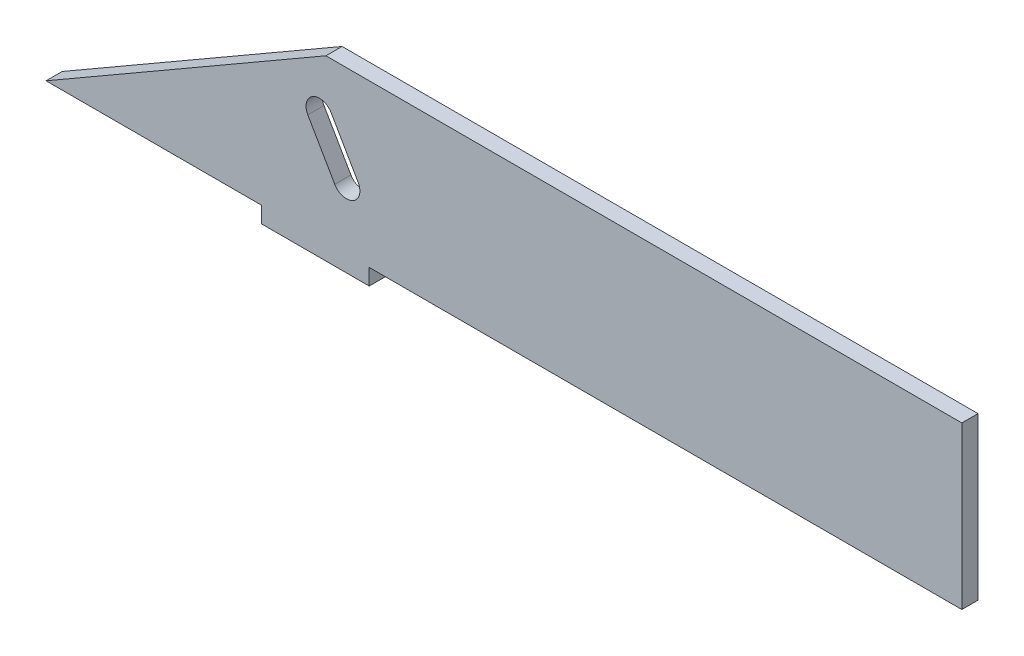
SolidWorks part; units mm, degrees
ref_plane "Front Plane" through (0, 0, 0) normal (0, 0, 1) x (1, 0, 0)
ref_plane "Top Plane" through (0, 0, 0) normal (0, 1, 0) x (1, 0, 0)
ref_plane "Right Plane" through (0, 0, 0) normal (1, 0, 0) x (0, 0, -1)
sketch "Sketch1" plane through (0, 0, 0) normal (0, 0, 1) x (1, 0, 0)
  line L0 (-10, -15) -> (-10, -18)
  line L1 (50, -15) -> (10, -15)
  line L2 (50, -15) -> (50, 15)
  line L3 (50, 15) -> (-50, 15)
  line L4 (-50, -15) -> (-50, 15)
  line L5 (50, -15) -> (-50, 15) construction
  line L6 (50, 15) -> (-50, -15) construction
  line L7 (-10, -18) -> (10, -18)
  line L8 (10, -18) -> (10, -15)
  line L9 (-10, -15) -> (-50, -15)
  point P0 (0, 0)
  dimension "D1" = 100
  dimension "D2" = 30
  dimension "D3" = 3
  dimension "D4" = 20
  dimension "D5" = 40
extrude "Boss-Extrude1" add sketch "Sketch1" along normal blind 3
sketch "Sketch4" plane through (0, 0, 3) normal (0, 0, 1) x (1, 0, 0)
  line L0 (-50, -15) -> (1.9615, 15)
  line L1 (50, 15) -> (-50, 15) construction
  line L2 (-50, 15) -> (-50, -15) construction
  line L3 (1.9615, 15) -> (-50, 15)
  line L4 (-50, 15) -> (-50, -14.2203)
  dimension "D1" = 60
extrude "Cut-Extrude3" cut sketch "Sketch4" against normal blind 3 and the other way through all
sketch "Sketch5" plane through (0, 0, 3) normal (0, 0, 1) x (1, 0, 0)
  line L0 (1.9615, 15) -> (13.7259, -5.3765) construction
  line L1 (-50, -15) -> (1.9615, 15) construction
  line L2 (-3.2346, 12) -> (8.5298, -8.3765) construction
  line L3 (7.9304, -2.3385) -> (2.9304, 6.3218)
  line L4 (3.6003, -4.8385) -> (-1.3997, 3.8218)
  arc A0 (3.6003, -4.8385) -> (7.9304, -2.3385) centre (5.7654, -3.5885) ccw
  arc A1 (2.9304, 6.3218) -> (-1.3997, 3.8218) centre (0.7654, 5.0718) ccw
  dimension "D2" = 5
  dimension "D3" = 5
  dimension "D4" = 8
  dimension "10" = 10
  dimension "D1" = 6
extrude "Cut-Extrude4" cut sketch "Sketch5" against normal blind 4
sketch "Sketch6" plane through (50, 0, 0) normal (1, 0, 0) x (0, 0, -1)
  line L0 (-3, 15) -> (0, 15) construction
  line L1 (-3, 15) -> (0, 15)
  line L2 (-3, -15) -> (-3, 15) construction
  line L3 (-3, -15) -> (-3, 15)
  line L4 (0, -15) -> (0, 15) construction
  line L5 (0, -15) -> (0, 15)
  line L6 (-3, -15) -> (0, -15) construction
  line L7 (-3, -15) -> (0, -15)
extrude "Boss-Extrude2" add sketch "Sketch6" along normal blind 70
